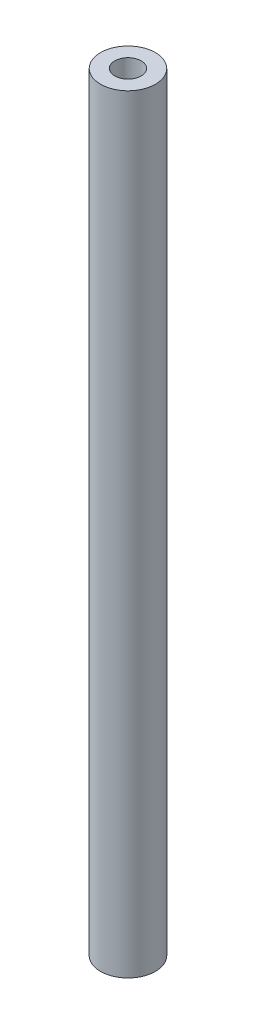
SolidWorks part; units mm, degrees
material "AISI Type 316L stainless steel"
ref_plane "Front Plane" through (0, 0, 0) normal (0, 0, 1) x (1, 0, 0)
ref_plane "Top Plane" through (0, 0, 0) normal (0, 1, 0) x (1, 0, 0)
ref_plane "Right Plane" through (0, 0, 0) normal (1, 0, 0) x (0, 0, -1)
sketch "Sketch1" plane through (0, 0, 0) normal (0, 1, 0) x (1, 0, 0)
  circle A0 centre (0, 0) radius 3.175
  circle A1 centre (0, 0) radius 1.524
  dimension "D1" = 6.35
  dimension "D2" = 3.048
extrude "Boss-Extrude1" add sketch "Sketch1" along normal blind 88.9
